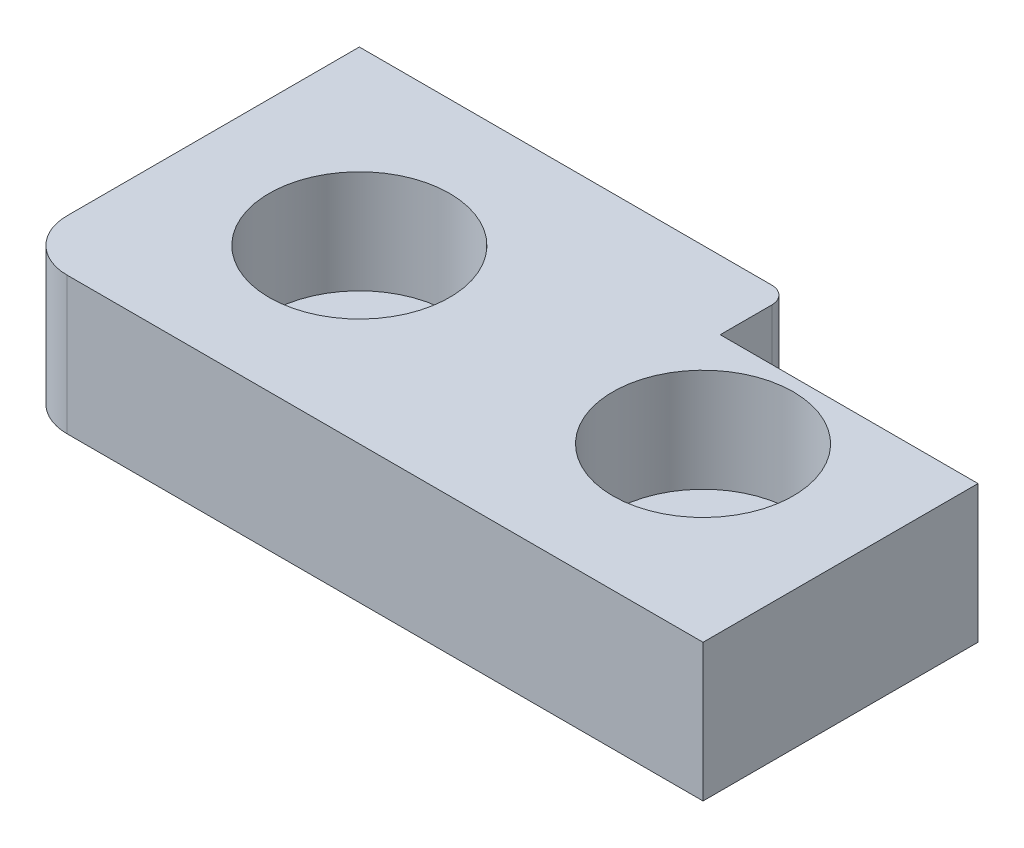
SolidWorks part; units mm, degrees
ref_plane "Front Plane" through (0, 0, 0) normal (0, 0, 1) x (1, 0, 0)
ref_plane "Top Plane" through (0, 0, 0) normal (0, 1, 0) x (1, 0, 0)
ref_plane "Right Plane" through (0, 0, 0) normal (1, 0, 0) x (0, 0, -1)
sketch "Sketch1" plane through (0, 0, 0) normal (0, 1, 0) x (1, 0, 0)
  line L0 (25, 20) -> (25, 0) construction
  line L1 (3, 0) -> (37, 0)
  line L2 (0, 3) -> (0, 20)
  line L3 (0, 20) -> (24, 20)
  line L4 (40, 3) -> (40, 16)
  line L5 (35, 20) -> (35, 0) construction
  line L6 (25, 19) -> (25, 16)
  line L7 (25, 16) -> (40, 16)
  line L8 (10, 20) -> (10, 0) construction
  line L9 (30, 20) -> (30, 0) construction
  line L10 (37, 0) -> (40, 0)
  line L11 (40, 0) -> (40, 3)
  arc A1 (3, 0) -> (0, 3) centre (3, 3) cw
  arc A2 (25, 19) -> (24, 20) centre (24, 19) ccw
  point P14 (0, 0)
  dimension "D7" = 1
  dimension "D1" = 20
  dimension "D2" = 40
  dimension "D3" = 15
  dimension "D4" = 5
  dimension "D5" = 4
  dimension "D8" = 10
  dimension "D9" = 30
extrude "Boss-Extrude1" add sketch "Sketch1" along normal blind 8
hole_wizard "CBORE for M5 SHCS1" positions "Sketch3" profile "Sketch2" counterbore size "M5" standard "ANSI Metric" end condition up to next
sketch "Sketch3" plane through (0, 8, 0) normal (0, 1, 0) x (1, 0, 0)
  line L0 (10, 20) -> (10, 0) construction
  line L2 (30, 20) -> (30, 0) construction
  point P0 (30, 10)
  point P2 (10, 10)
sketch "Sketch2" plane through (30, 8, -10) normal (1, 0, 0) x (0, 0, 1)
  line L0 (0, 0) -> (0, 8)
  line L1 (0, 8) -> (2.75, 8)
  line L3 (2.75, 8) -> (2.75, 6)
  line L4 (2.75, 6) -> (5.25, 6)
  line L5 (5.25, 6) -> (5.25, 0)
  line L7 (5.25, 0) -> (0, 0)
  line L11 (0, -6.35) -> (0, 107.95) construction
  dimension "Thru Hole Dia." = 5.5
  dimension "Thru Hole Depth" = 8
  dimension "C'Bore Dia." = 10.5
  dimension "C'Bore Depth" = 6
sketch "Sketch4" plane through (0, 0, 0) normal (0, 1, 0) x (1, 0, 0)
  line L1 (36, 16) -> (55.8, 16)
  line L2 (36, 16) -> (36, 0)
  line L3 (36, 0) -> (55.8, 0)
  line L4 (55.8, 16) -> (55.8, 0)
  line L6 (25, 16) -> (40, 16) construction
  line L7 (3, 0) -> (37, 0) construction
  circle A0 centre (30, 10) radius 5.25 construction
  dimension "D3" = 6
  dimension "D2" = 19.8
